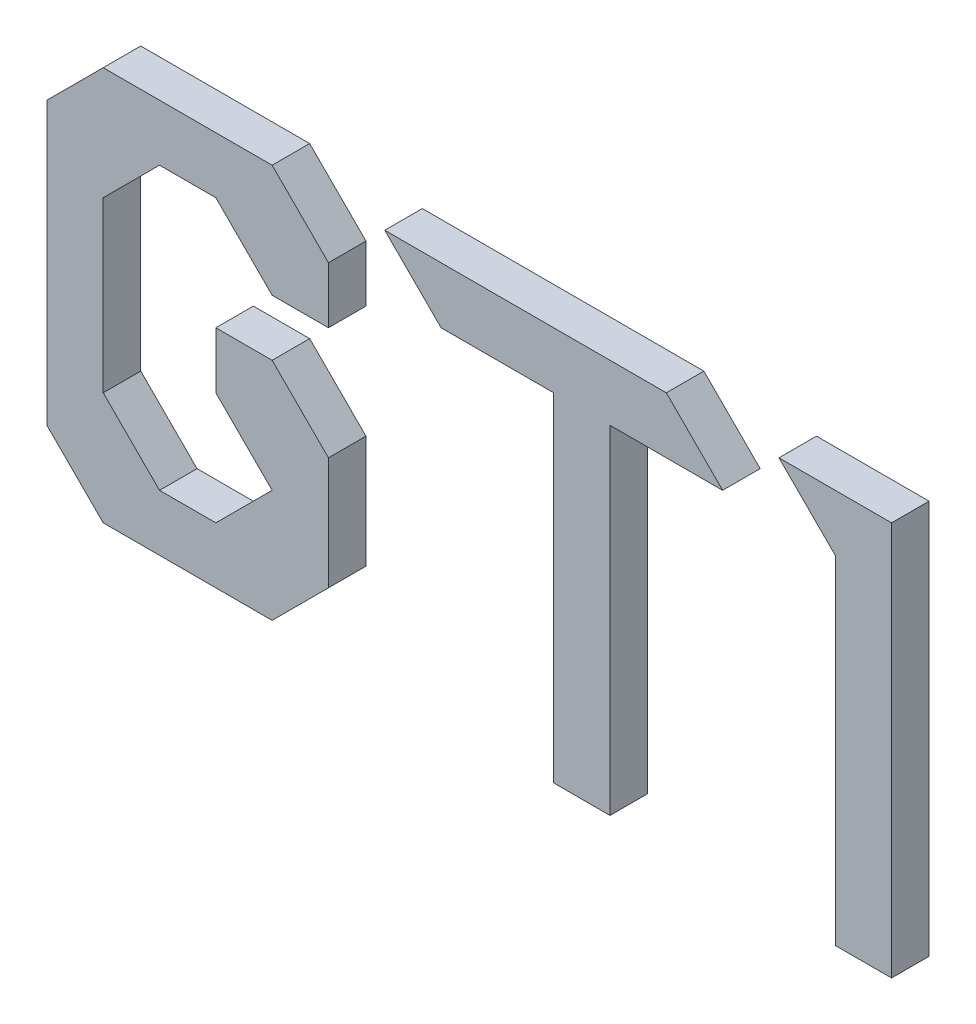
SolidWorks part; units mm, degrees
ref_plane "Front Plane" through (0, 0, 0) normal (0, 0, 1) x (1, 0, 0)
ref_plane "Top Plane" through (0, 0, 0) normal (0, 1, 0) x (1, 0, 0)
ref_plane "Right Plane" through (0, 0, 0) normal (1, 0, 0) x (0, 0, -1)
sketch "Sketch1" plane through (0, 0, 0) normal (0, 0, 1) x (1, 0, 0)
  line L0 (15, 15) -> (30, 15)
  line L1 (0, 0) -> (15, 0)
  line L2 (0, 0) -> (0, 15)
  line L3 (0, 15) -> (15, 15)
  line L4 (15, 0) -> (15, 15)
  line L5 (30, 0) -> (30, 15)
  line L6 (15, 0) -> (15, 15)
  line L7 (15, 0) -> (30, 0)
  line L8 (30, 15) -> (45, 15)
  line L9 (45, 0) -> (45, 15)
  line L10 (30, 0) -> (30, 15)
  line L11 (30, 0) -> (45, 0)
  line L12 (45, 15) -> (60, 15)
  line L13 (60, 0) -> (60, 15)
  line L14 (45, 0) -> (45, 15)
  line L15 (45, 0) -> (60, 0)
  line L16 (60, 15) -> (75, 15)
  line L17 (75, 0) -> (75, 15)
  line L18 (60, 0) -> (60, 15)
  line L19 (60, 0) -> (75, 0)
  line L20 (75, 15) -> (90, 15)
  line L21 (90, 0) -> (90, 15)
  line L22 (75, 0) -> (75, 15)
  line L23 (75, 0) -> (90, 0)
  line L24 (90, 15) -> (105, 15)
  line L25 (105, 0) -> (105, 15)
  line L26 (90, 0) -> (90, 15)
  line L27 (90, 0) -> (105, 0)
  line L28 (105, 15) -> (120, 15)
  line L29 (120, 0) -> (120, 15)
  line L30 (105, 0) -> (105, 15)
  line L31 (105, 0) -> (120, 0)
  line L32 (120, 15) -> (135, 15)
  line L33 (135, 0) -> (135, 15)
  line L34 (120, 0) -> (120, 15)
  line L35 (120, 0) -> (135, 0)
  line L36 (135, 15) -> (150, 15)
  line L37 (150, 0) -> (150, 15)
  line L38 (135, 0) -> (135, 15)
  line L39 (135, 0) -> (150, 0)
  line L40 (150, 15) -> (165, 15)
  line L41 (165, 0) -> (165, 15)
  line L42 (150, 0) -> (150, 15)
  line L43 (150, 0) -> (165, 0)
  line L44 (165, 15) -> (180, 15)
  line L45 (180, 0) -> (180, 15)
  line L46 (165, 0) -> (165, 15)
  line L47 (165, 0) -> (180, 0)
  line L48 (180, 15) -> (195, 15)
  line L49 (195, 0) -> (195, 15)
  line L50 (180, 0) -> (180, 15)
  line L51 (180, 0) -> (195, 0)
  line L52 (195, 15) -> (210, 15)
  line L53 (210, 0) -> (210, 15)
  line L54 (195, 0) -> (195, 15)
  line L55 (195, 0) -> (210, 0)
  line L56 (210, 15) -> (225, 15)
  line L57 (225, 0) -> (225, 15)
  line L58 (210, 0) -> (210, 15)
  line L59 (210, 0) -> (225, 0)
  line L60 (0, 30) -> (15, 30)
  line L61 (15, 15) -> (15, 30)
  line L62 (0, 15) -> (0, 30)
  line L63 (0, 15) -> (15, 15)
  line L64 (15, 30) -> (30, 30)
  line L65 (30, 15) -> (30, 30)
  line L66 (15, 15) -> (15, 30)
  line L67 (15, 15) -> (30, 15)
  line L68 (30, 30) -> (45, 30)
  line L69 (45, 15) -> (45, 30)
  line L70 (30, 15) -> (30, 30)
  line L71 (30, 15) -> (45, 15)
  line L72 (45, 30) -> (60, 30)
  line L73 (60, 15) -> (60, 30)
  line L74 (45, 15) -> (45, 30)
  line L75 (45, 15) -> (60, 15)
  line L76 (60, 30) -> (75, 30)
  line L77 (75, 15) -> (75, 30)
  line L78 (60, 15) -> (60, 30)
  line L79 (60, 15) -> (75, 15)
  line L80 (75, 30) -> (90, 30)
  line L81 (90, 15) -> (90, 30)
  line L82 (75, 15) -> (75, 30)
  line L83 (75, 15) -> (90, 15)
  line L84 (90, 30) -> (105, 30)
  line L85 (105, 15) -> (105, 30)
  line L86 (90, 15) -> (90, 30)
  line L87 (90, 15) -> (105, 15)
  line L88 (105, 30) -> (120, 30)
  line L89 (120, 15) -> (120, 30)
  line L90 (105, 15) -> (105, 30)
  line L91 (105, 15) -> (120, 15)
  line L92 (120, 30) -> (135, 30)
  line L93 (135, 15) -> (135, 30)
  line L94 (120, 15) -> (120, 30)
  line L95 (120, 15) -> (135, 15)
  line L96 (135, 30) -> (150, 30)
  line L97 (150, 15) -> (150, 30)
  line L98 (135, 15) -> (135, 30)
  line L99 (135, 15) -> (150, 15)
  line L100 (150, 30) -> (165, 30)
  line L101 (165, 15) -> (165, 30)
  line L102 (150, 15) -> (150, 30)
  line L103 (150, 15) -> (165, 15)
  line L104 (165, 30) -> (180, 30)
  line L105 (180, 15) -> (180, 30)
  line L106 (165, 15) -> (165, 30)
  line L107 (165, 15) -> (180, 15)
  line L108 (180, 30) -> (195, 30)
  line L109 (195, 15) -> (195, 30)
  line L110 (180, 15) -> (180, 30)
  line L111 (180, 15) -> (195, 15)
  line L112 (195, 30) -> (210, 30)
  line L113 (210, 15) -> (210, 30)
  line L114 (195, 15) -> (195, 30)
  line L115 (195, 15) -> (210, 15)
  line L116 (210, 30) -> (225, 30)
  line L117 (225, 15) -> (225, 30)
  line L118 (210, 15) -> (210, 30)
  line L119 (210, 15) -> (225, 15)
  line L120 (0, 45) -> (15, 45)
  line L121 (15, 30) -> (15, 45)
  line L122 (0, 30) -> (0, 45)
  line L123 (0, 30) -> (15, 30)
  line L124 (15, 45) -> (30, 45)
  line L125 (30, 30) -> (30, 45)
  line L126 (15, 30) -> (15, 45)
  line L127 (15, 30) -> (30, 30)
  line L128 (30, 45) -> (45, 45)
  line L129 (45, 30) -> (45, 45)
  line L130 (30, 30) -> (30, 45)
  line L131 (30, 30) -> (45, 30)
  line L132 (45, 45) -> (60, 45)
  line L133 (60, 30) -> (60, 45)
  line L134 (45, 30) -> (45, 45)
  line L135 (45, 30) -> (60, 30)
  line L136 (60, 45) -> (75, 45)
  line L137 (75, 30) -> (75, 45)
  line L138 (60, 30) -> (60, 45)
  line L139 (60, 30) -> (75, 30)
  line L140 (75, 45) -> (90, 45)
  line L141 (90, 30) -> (90, 45)
  line L142 (75, 30) -> (75, 45)
  line L143 (75, 30) -> (90, 30)
  line L144 (90, 45) -> (105, 45)
  line L145 (105, 30) -> (105, 45)
  line L146 (90, 30) -> (90, 45)
  line L147 (90, 30) -> (105, 30)
  line L148 (105, 45) -> (120, 45)
  line L149 (120, 30) -> (120, 45)
  line L150 (105, 30) -> (105, 45)
  line L151 (105, 30) -> (120, 30)
  line L152 (120, 45) -> (135, 45)
  line L153 (135, 30) -> (135, 45)
  line L154 (120, 30) -> (120, 45)
  line L155 (120, 30) -> (135, 30)
  line L156 (135, 45) -> (150, 45)
  line L157 (150, 30) -> (150, 45)
  line L158 (135, 30) -> (135, 45)
  line L159 (135, 30) -> (150, 30)
  line L160 (150, 45) -> (165, 45)
  line L161 (165, 30) -> (165, 45)
  line L162 (150, 30) -> (150, 45)
  line L163 (150, 30) -> (165, 30)
  line L164 (165, 45) -> (180, 45)
  line L165 (180, 30) -> (180, 45)
  line L166 (165, 30) -> (165, 45)
  line L167 (165, 30) -> (180, 30)
  line L168 (180, 45) -> (195, 45)
  line L169 (195, 30) -> (195, 45)
  line L170 (180, 30) -> (180, 45)
  line L171 (180, 30) -> (195, 30)
  line L172 (195, 45) -> (210, 45)
  line L173 (210, 30) -> (210, 45)
  line L174 (195, 30) -> (195, 45)
  line L175 (195, 30) -> (210, 30)
  line L176 (210, 45) -> (225, 45)
  line L177 (225, 30) -> (225, 45)
  line L178 (210, 30) -> (210, 45)
  line L179 (210, 30) -> (225, 30)
  line L180 (0, 60) -> (15, 60)
  line L181 (15, 45) -> (15, 60)
  line L182 (0, 45) -> (0, 60)
  line L183 (0, 45) -> (15, 45)
  line L184 (15, 60) -> (30, 60)
  line L185 (30, 45) -> (30, 60)
  line L186 (15, 45) -> (15, 60)
  line L187 (15, 45) -> (30, 45)
  line L188 (30, 60) -> (45, 60)
  line L189 (45, 45) -> (45, 60)
  line L190 (30, 45) -> (30, 60)
  line L191 (30, 45) -> (45, 45)
  line L192 (45, 60) -> (60, 60)
  line L193 (60, 45) -> (60, 60)
  line L194 (45, 45) -> (45, 60)
  line L195 (45, 45) -> (60, 45)
  line L196 (60, 60) -> (75, 60)
  line L197 (75, 45) -> (75, 60)
  line L198 (60, 45) -> (60, 60)
  line L199 (60, 45) -> (75, 45)
  line L200 (75, 60) -> (90, 60)
  line L201 (90, 45) -> (90, 60)
  line L202 (75, 45) -> (75, 60)
  line L203 (75, 45) -> (90, 45)
  line L204 (90, 60) -> (105, 60)
  line L205 (105, 45) -> (105, 60)
  line L206 (90, 45) -> (90, 60)
  line L207 (90, 45) -> (105, 45)
  line L208 (105, 60) -> (120, 60)
  line L209 (120, 45) -> (120, 60)
  line L210 (105, 45) -> (105, 60)
  line L211 (105, 45) -> (120, 45)
  line L212 (120, 60) -> (135, 60)
  line L213 (135, 45) -> (135, 60)
  line L214 (120, 45) -> (120, 60)
  line L215 (120, 45) -> (135, 45)
  line L216 (135, 60) -> (150, 60)
  line L217 (150, 45) -> (150, 60)
  line L218 (135, 45) -> (135, 60)
  line L219 (135, 45) -> (150, 45)
  line L220 (150, 60) -> (165, 60)
  line L221 (165, 45) -> (165, 60)
  line L222 (150, 45) -> (150, 60)
  line L223 (150, 45) -> (165, 45)
  line L224 (165, 60) -> (180, 60)
  line L225 (180, 45) -> (180, 60)
  line L226 (165, 45) -> (165, 60)
  line L227 (165, 45) -> (180, 45)
  line L228 (180, 60) -> (195, 60)
  line L229 (195, 45) -> (195, 60)
  line L230 (180, 45) -> (180, 60)
  line L231 (180, 45) -> (195, 45)
  line L232 (195, 60) -> (210, 60)
  line L233 (210, 45) -> (210, 60)
  line L234 (195, 45) -> (195, 60)
  line L235 (195, 45) -> (210, 45)
  line L236 (210, 60) -> (225, 60)
  line L237 (225, 45) -> (225, 60)
  line L238 (210, 45) -> (210, 60)
  line L239 (210, 45) -> (225, 45)
  line L240 (0, 75) -> (15, 75)
  line L241 (15, 60) -> (15, 75)
  line L242 (0, 60) -> (0, 75)
  line L243 (0, 60) -> (15, 60)
  line L244 (15, 75) -> (30, 75)
  line L245 (30, 60) -> (30, 75)
  line L246 (15, 60) -> (15, 75)
  line L247 (15, 60) -> (30, 60)
  line L248 (30, 75) -> (45, 75)
  line L249 (45, 60) -> (45, 75)
  line L250 (30, 60) -> (30, 75)
  line L251 (30, 60) -> (45, 60)
  line L252 (45, 75) -> (60, 75)
  line L253 (60, 60) -> (60, 75)
  line L254 (45, 60) -> (45, 75)
  line L255 (45, 60) -> (60, 60)
  line L256 (60, 75) -> (75, 75)
  line L257 (75, 60) -> (75, 75)
  line L258 (60, 60) -> (60, 75)
  line L259 (60, 60) -> (75, 60)
  line L260 (75, 75) -> (90, 75)
  line L261 (90, 60) -> (90, 75)
  line L262 (75, 60) -> (75, 75)
  line L263 (75, 60) -> (90, 60)
  line L264 (90, 75) -> (105, 75)
  line L265 (105, 60) -> (105, 75)
  line L266 (90, 60) -> (90, 75)
  line L267 (90, 60) -> (105, 60)
  line L268 (105, 75) -> (120, 75)
  line L269 (120, 60) -> (120, 75)
  line L270 (105, 60) -> (105, 75)
  line L271 (105, 60) -> (120, 60)
  line L272 (120, 75) -> (135, 75)
  line L273 (135, 60) -> (135, 75)
  line L274 (120, 60) -> (120, 75)
  line L275 (120, 60) -> (135, 60)
  line L276 (135, 75) -> (150, 75)
  line L277 (150, 60) -> (150, 75)
  line L278 (135, 60) -> (135, 75)
  line L279 (135, 60) -> (150, 60)
  line L280 (150, 75) -> (165, 75)
  line L281 (165, 60) -> (165, 75)
  line L282 (150, 60) -> (150, 75)
  line L283 (150, 60) -> (165, 60)
  line L284 (165, 75) -> (180, 75)
  line L285 (180, 60) -> (180, 75)
  line L286 (165, 60) -> (165, 75)
  line L287 (165, 60) -> (180, 60)
  line L288 (180, 75) -> (195, 75)
  line L289 (195, 60) -> (195, 75)
  line L290 (180, 60) -> (180, 75)
  line L291 (180, 60) -> (195, 60)
  line L292 (195, 75) -> (210, 75)
  line L293 (210, 60) -> (210, 75)
  line L294 (195, 60) -> (195, 75)
  line L295 (195, 60) -> (210, 60)
  line L296 (210, 75) -> (225, 75)
  line L297 (225, 60) -> (225, 75)
  line L298 (210, 60) -> (210, 75)
  line L299 (210, 60) -> (225, 60)
  line L300 (0, 90) -> (15, 90)
  line L301 (15, 75) -> (15, 90)
  line L302 (0, 75) -> (0, 90)
  line L303 (0, 75) -> (15, 75)
  line L304 (15, 90) -> (30, 90)
  line L305 (30, 75) -> (30, 90)
  line L306 (15, 75) -> (15, 90)
  line L307 (15, 75) -> (30, 75)
  line L308 (30, 90) -> (45, 90)
  line L309 (45, 75) -> (45, 90)
  line L310 (30, 75) -> (30, 90)
  line L311 (30, 75) -> (45, 75)
  line L312 (45, 90) -> (60, 90)
  line L313 (60, 75) -> (60, 90)
  line L314 (45, 75) -> (45, 90)
  line L315 (45, 75) -> (60, 75)
  line L316 (60, 90) -> (75, 90)
  line L317 (75, 75) -> (75, 90)
  line L318 (60, 75) -> (60, 90)
  line L319 (60, 75) -> (75, 75)
  line L320 (75, 90) -> (90, 90)
  line L321 (90, 75) -> (90, 90)
  line L322 (75, 75) -> (75, 90)
  line L323 (75, 75) -> (90, 75)
  line L324 (90, 90) -> (105, 90)
  line L325 (105, 75) -> (105, 90)
  line L326 (90, 75) -> (90, 90)
  line L327 (90, 75) -> (105, 75)
  line L328 (105, 90) -> (120, 90)
  line L329 (120, 75) -> (120, 90)
  line L330 (105, 75) -> (105, 90)
  line L331 (105, 75) -> (120, 75)
  line L332 (120, 90) -> (135, 90)
  line L333 (135, 75) -> (135, 90)
  line L334 (120, 75) -> (120, 90)
  line L335 (120, 75) -> (135, 75)
  line L336 (135, 90) -> (150, 90)
  line L337 (150, 75) -> (150, 90)
  line L338 (135, 75) -> (135, 90)
  line L339 (135, 75) -> (150, 75)
  line L340 (150, 90) -> (165, 90)
  line L341 (165, 75) -> (165, 90)
  line L342 (150, 75) -> (150, 90)
  line L343 (150, 75) -> (165, 75)
  line L344 (165, 90) -> (180, 90)
  line L345 (180, 75) -> (180, 90)
  line L346 (165, 75) -> (165, 90)
  line L347 (165, 75) -> (180, 75)
  line L348 (180, 90) -> (195, 90)
  line L349 (195, 75) -> (195, 90)
  line L350 (180, 75) -> (180, 90)
  line L351 (180, 75) -> (195, 75)
  line L352 (195, 90) -> (210, 90)
  line L353 (210, 75) -> (210, 90)
  line L354 (195, 75) -> (195, 90)
  line L355 (195, 75) -> (210, 75)
  line L356 (210, 90) -> (225, 90)
  line L357 (225, 75) -> (225, 90)
  line L358 (210, 75) -> (210, 90)
  line L359 (210, 75) -> (225, 75)
  line L360 (0, 105) -> (15, 105)
  line L361 (15, 90) -> (15, 105)
  line L362 (0, 90) -> (0, 105)
  line L363 (0, 90) -> (15, 90)
  line L364 (15, 105) -> (30, 105)
  line L365 (30, 90) -> (30, 105)
  line L366 (15, 90) -> (15, 105)
  line L367 (15, 90) -> (30, 90)
  line L368 (30, 105) -> (45, 105)
  line L369 (45, 90) -> (45, 105)
  line L370 (30, 90) -> (30, 105)
  line L371 (30, 90) -> (45, 90)
  line L372 (45, 105) -> (60, 105)
  line L373 (60, 90) -> (60, 105)
  line L374 (45, 90) -> (45, 105)
  line L375 (45, 90) -> (60, 90)
  line L376 (60, 105) -> (75, 105)
  line L377 (75, 90) -> (75, 105)
  line L378 (60, 90) -> (60, 105)
  line L379 (60, 90) -> (75, 90)
  line L380 (75, 105) -> (90, 105)
  line L381 (90, 90) -> (90, 105)
  line L382 (75, 90) -> (75, 105)
  line L383 (75, 90) -> (90, 90)
  line L384 (90, 105) -> (105, 105)
  line L385 (105, 90) -> (105, 105)
  line L386 (90, 90) -> (90, 105)
  line L387 (90, 90) -> (105, 90)
  line L388 (105, 105) -> (120, 105)
  line L389 (120, 90) -> (120, 105)
  line L390 (105, 90) -> (105, 105)
  line L391 (105, 90) -> (120, 90)
  line L392 (120, 105) -> (135, 105)
  line L393 (135, 90) -> (135, 105)
  line L394 (120, 90) -> (120, 105)
  line L395 (120, 90) -> (135, 90)
  line L396 (135, 105) -> (150, 105)
  line L397 (150, 90) -> (150, 105)
  line L398 (135, 90) -> (135, 105)
  line L399 (135, 90) -> (150, 90)
  line L400 (150, 105) -> (165, 105)
  line L401 (165, 90) -> (165, 105)
  line L402 (150, 90) -> (150, 105)
  line L403 (150, 90) -> (165, 90)
  line L404 (165, 105) -> (180, 105)
  line L405 (180, 90) -> (180, 105)
  line L406 (165, 90) -> (165, 105)
  line L407 (165, 90) -> (180, 90)
  line L408 (180, 105) -> (195, 105)
  line L409 (195, 90) -> (195, 105)
  line L410 (180, 90) -> (180, 105)
  line L411 (180, 90) -> (195, 90)
  line L412 (195, 105) -> (210, 105)
  line L413 (210, 90) -> (210, 105)
  line L414 (195, 90) -> (195, 105)
  line L415 (195, 90) -> (210, 90)
  line L416 (210, 105) -> (225, 105)
  line L417 (225, 90) -> (225, 105)
  line L418 (210, 90) -> (210, 105)
  line L419 (210, 90) -> (225, 90)
  dimension "D1" = 15
  dimension "D2" = 15
sketch "Sketch2" plane through (0, 0, 0) normal (0, 0, 1) x (1, 0, 0)
  line L0 (60, 0) -> (15, 0)
  line L1 (15, 0) -> (0, 15)
  line L2 (0, 15) -> (0, 90)
  line L3 (0, 90) -> (15, 105)
  line L4 (15, 105) -> (60, 105)
  line L5 (60, 105) -> (75, 90)
  line L6 (75, 90) -> (75, 75)
  line L7 (75, 75) -> (60, 75)
  line L8 (60, 75) -> (45, 90)
  line L9 (45, 90) -> (30, 90)
  line L10 (30, 90) -> (15, 75)
  line L11 (15, 75) -> (15, 30)
  line L12 (15, 30) -> (30, 15)
  line L13 (30, 15) -> (45, 15)
  line L14 (45, 15) -> (60, 30)
  line L15 (60, 30) -> (45, 45)
  line L16 (45, 45) -> (45, 60)
  line L17 (45, 60) -> (60, 60)
  line L18 (60, 60) -> (75, 45)
  line L19 (75, 45) -> (75, 15)
  line L20 (75, 15) -> (60, 0)
  line L21 (90, 105) -> (105, 90)
  line L22 (105, 90) -> (120, 90)
  line L23 (120, 90) -> (135, 90)
  line L25 (135, 0) -> (135, 90)
  line L26 (135, 90) -> (165, 90)
  line L27 (150, 90) -> (150, 0)
  line L28 (150, 105) -> (90, 105)
  line L29 (195, 105) -> (210, 90)
  line L30 (210, 90) -> (210, 0)
  line L31 (210, 0) -> (225, 0)
  line L32 (225, 0) -> (225, 105)
  line L33 (225, 105) -> (195, 105)
  line L34 (150, 105) -> (165, 105)
  line L35 (165, 105) -> (180, 90)
  line L36 (180, 90) -> (165, 90)
  line L37 (150, 0) -> (135, 0)
extrude "Extrude1" add sketch "Sketch2" along normal blind 10 contours L20 L19 L18 L17 L16 L15 L14 L13 L12 L11 L10 L9 L8 L7 L6 L5 L4 L3 L2 L1 L0 | L36 L35 L34 L28 L21 L22 L23 L26 | L32 L33 L29 L30 L31 | L37 L27 L26 L25
